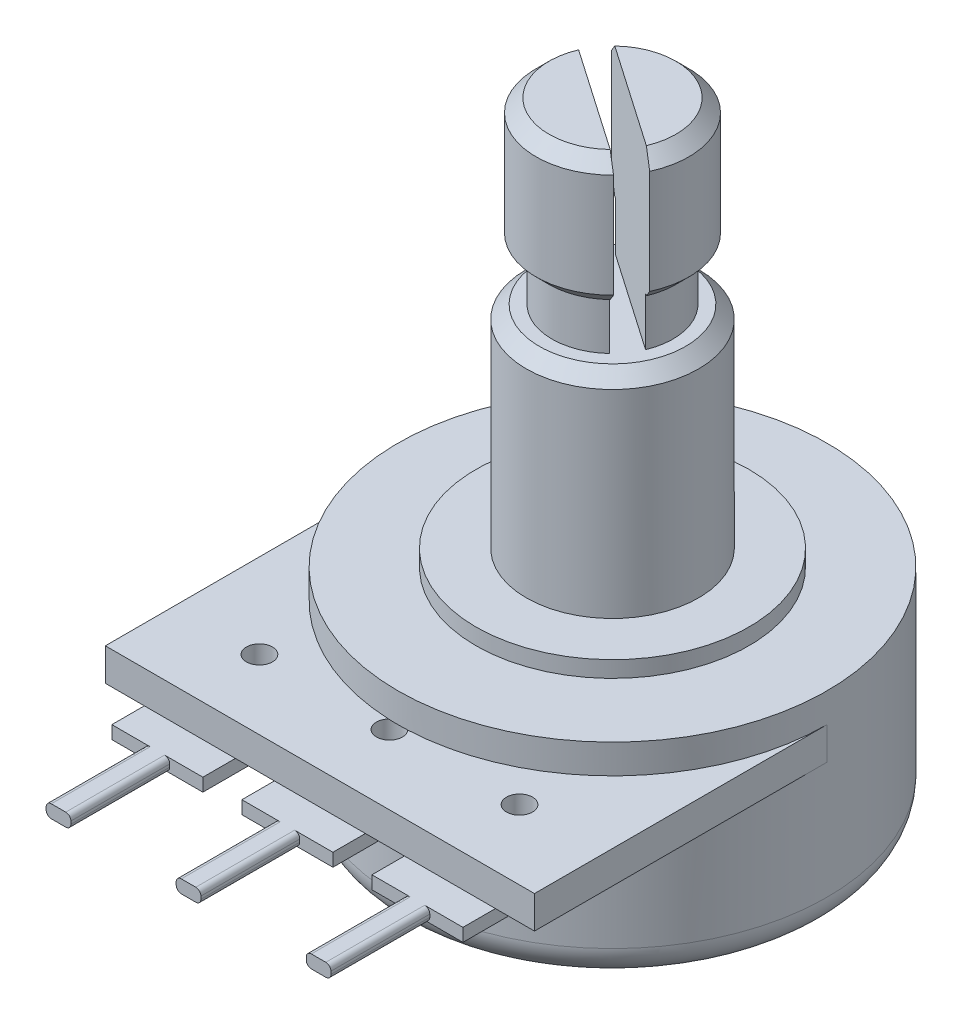
SolidWorks part; units mm, degrees
ref_plane "Front" through (0, 0, 0) normal (0, 0, 1) x (1, 0, 0)
ref_plane "Side" through (0, 0, 0) normal (0, 1, 0) x (1, 0, 0)
ref_plane "Top" through (0, 0, 0) normal (1, 0, 0) x (0, 0, -1)
sketch "Sketch1" plane through (0, 0, 0) normal (0, 0, 1) x (1, 0, 0)
  line L0 (0, 0) -> (8.382, 0)
  line L1 (8.382, 0) -> (8.382, 8.89)
  line L2 (8.382, 8.89) -> (3.3655, 8.89)
  line L3 (3.3655, 8.89) -> (3.3655, 17.145)
  line L4 (3.3655, 17.145) -> (2.3622, 17.145)
  line L5 (2.3622, 17.145) -> (2.3622, 19.05)
  line L6 (2.3622, 19.05) -> (2.9845, 19.05)
  line L7 (2.9845, 19.05) -> (2.9845, 24.13)
  line L8 (2.9845, 24.13) -> (0, 24.13)
  line L9 (0, 24.13) -> (0, 0)
  line L10 (0, 0) -> (0, -13.97) construction
  dimension "D1" = 24.13
  dimension "D2" = 5.08
  dimension "D3" = 15.24
  dimension "D4" = 1.905
  dimension "D5" = 2.9845
  dimension "D6" = 2.3622
  dimension "D7" = 3.3655
  dimension "D8" = 8.382
revolve "Base-Revolve" add sketch "Sketch1" angle 360 about L10
sketch "Sketch2" plane through (0, 0, 0) normal (0, 0, 1) x (1, 0, 0)
  line L0 (-8.382, 7.112) -> (8.382, 7.112)
  line L1 (-8.382, 7.112) -> (-8.382, 5.842)
  line L2 (8.382, 5.842) -> (-8.382, 5.842)
  line L3 (8.382, 5.842) -> (8.382, 7.112)
  line L5 (8.382, 0) -> (8.382, 8.89) construction
  line L6 (-8.382, 8.89) -> (-8.382, 0) construction
  line L7 (-8.382, 0) -> (8.382, 0) construction
  dimension "D1" = 1.27
  dimension "D2" = 5.842
extrude "Boss-Extrude1" add sketch "Sketch2" along normal blind 11.43
sketch "Sketch3" plane through (0, 5.842, 0) normal (0, -1, 0) x (1, 0, 0)
  line L0 (-1.778, 12.7) -> (-0.4826, 12.7)
  line L1 (-1.778, 12.7) -> (-1.778, 8.7122)
  line L3 (1.778, 8.7122) -> (1.778, 12.7)
  line L4 (0.4826, 12.7) -> (1.778, 12.7)
  line L5 (-0.4826, 12.7) -> (-0.4826, 16.5608)
  line L6 (0.4826, 16.5608) -> (-0.4826, 16.5608)
  line L7 (0.4826, 16.5608) -> (0.4826, 12.7)
  line L8 (0, 0) -> (0, 16.5608) construction
  circle A0 centre (0, 0) radius 8.382 construction
  arc A1 (-1.778, 8.7122) -> (1.778, 8.7122) centre (0, 8.7122) ccw
  circle A2 centre (0, 8.7122) radius 0.508
  dimension "D1" = 24.9428
  dimension "D3" = 12.7
  dimension "D5" = 5.7658
  dimension "D6" = 1.016
  dimension "D2" = 0.9652
  dimension "D4" = 3.556
extrude "Boss-Extrude2" add sketch "Sketch3" along normal blind 0.508
sketch "Sketch5" plane through (0, 24.13, 0) normal (0, 1, 0) x (-1, 0, 0)
  circle A0 centre (0, 0) radius 5.334
  circle A1 centre (0, 0) radius 8.382 construction
  circle A2 centre (0, 0) radius 8.382
  dimension "D1" = 10.668
extrude "Cut-Extrude2" cut sketch "Sketch5" against normal blind 15.875
pattern_linear "LPattern1" count 2 spacing 5.08 along (-1, 0, 0) of "Boss-Extrude2"
pattern_linear "LPattern2" count 2 spacing 5.08 along (1, 0, 0) of "Boss-Extrude2"
sketch "Sketch7" plane through (0, 5.842, 0) normal (0, -1, 0) x (1, 0, 0)
  circle A0 centre (-5.08, 8.7122) radius 0.508 construction
  circle A2 centre (5.08, 8.7122) radius 0.508 construction
  circle A3 centre (-5.08, 8.7122) radius 0.508
  circle A4 centre (0, 8.7122) radius 0.508
  circle A5 centre (5.08, 8.7122) radius 0.508
  arc A6 (0.3786, 8.3734) -> (-0.3786, 8.3734) centre (0, 8.7122) ccw construction
extrude "Cut-Extrude3" cut sketch "Sketch7" against normal up to surface (1.27 mm away) up to face at (0, 7.112, 7.8105)
sketch "Sketch8" plane through (0, 24.13, 0) normal (0, 1, 0) x (-1, 0, 0)
  line L0 (-2.7083, 1.254) -> (2.1307, -2.0898)
  line L1 (-2.1307, 2.0898) -> (2.7083, -1.254)
  line L2 (-3.7107, 2.5641) -> (3.7107, -2.5641) construction
  line L3 (0, 0) -> (4.6177, 0) construction
  circle A2 centre (0, 0) radius 2.9845 construction
  arc A3 (-2.1307, 2.0898) -> (-2.7083, 1.254) centre (0, 0) ccw
  arc A4 (2.1307, -2.0898) -> (2.7083, -1.254) centre (0, 0) ccw
  dimension "D1" = 0.508
  dimension "D2" = 1.016
  dimension "D3" = 145.355
extrude "Cut-Extrude4" cut sketch "Sketch8" against normal blind 6.985
chamfer "Chamfer1" distance 0.508 angle 45 5 edges at (1.6966, 24.13, -2.4553) (-1.6966, 24.13, 2.4553) (1.6966, 19.05, -2.4553) (-1.6966, 19.05, 2.4553) (0, 17.145, 3.3655)
fillet "Fillet1" radius 1.27 1 edges at (0, 0, 8.382)
fillet "Fillet2" radius 0.2 12 edges at (-5.5626, 5.842, 14.6304) (-4.5974, 5.842, 14.6304) (-4.5974, 5.334, 14.6304) (-5.5626, 5.334, 14.6304) (0.4826, 5.842, 14.6304) (0.4826, 5.334, 14.6304) (-0.4826, 5.842, 14.6304) (-0.4826, 5.334, 14.6304) (4.5974, 5.842, 14.6304) (4.5974, 5.334, 14.6304) (5.5626, 5.842, 14.6304) (5.5626, 5.334, 14.6304)
sketch "Sketch9" plane through (0, 0, 0) normal (0, -1, 0) x (1, 0, 0)
  line L0 (0, 0) -> (0, -10.2182) construction
  line L1 (-1, -5.6064) -> (1, -5.6064)
  line L2 (-1, -5.6064) -> (-1, -8.802)
  line L3 (-1, -8.802) -> (1, -8.802)
  line L4 (1, -5.6064) -> (1, -8.802)
  line L5 (0, -8.382) -> (1.9184, -8.3258) construction
  circle A0 centre (0, 0) radius 8.382 construction
  dimension "D1" = 1
  dimension "D2" = 1
extrude "Cut-Extrude5" cut sketch "Sketch9" against normal blind 2
fillet "Fillet3" radius 0.6 3 edges at (0, 2, -8.382) (0, 2, -5.6064) (0, 0, -5.6064)
